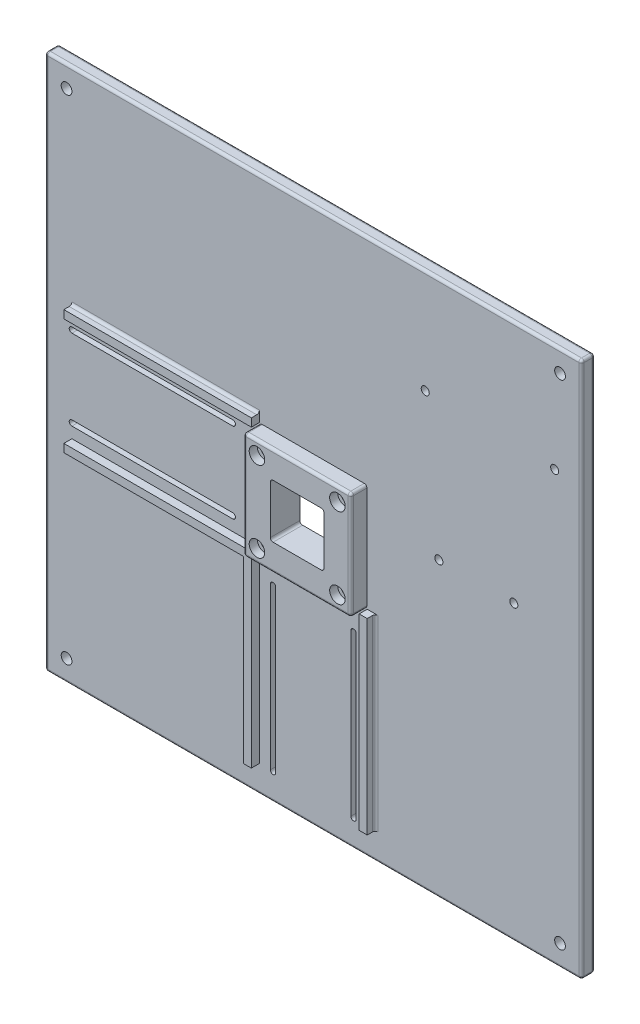
SolidWorks part; units mm, degrees
ref_plane "Plan de face" through (0, 0, 0) normal (0, 0, 1) x (1, 0, 0)
ref_plane "Plan de dessus" through (0, 0, 0) normal (0, 1, 0) x (1, 0, 0)
ref_plane "Plan de droite" through (0, 0, 0) normal (1, 0, 0) x (0, 0, -1)
sketch "Esquisse1" plane through (0, 0, 0) normal (0, 0, 1) x (1, 0, 0)
  line L1 (-100, 100) -> (100, 100)
  line L2 (-100, 100) -> (-100, -100)
  line L3 (-100, -100) -> (100, -100)
  line L4 (100, 100) -> (100, -100)
  dimension "D1" = 100
  dimension "D2" = 200
  dimension "D3" = 100
  dimension "D4" = 200
extrude "Boss.-Extru.1" add sketch "Esquisse1" along normal blind 5
fillet "Congé1" radius 1 12 edges at (0, -100, 5) (-100, 0, 5) (0, 100, 5) (100, 0, 5) (-100, -100, 2.5) (100, -100, 2.5) (-100, 100, 2.5) (100, 100, 2.5) (0, -100, 0) (-100, 0, 0) (0, 100, 0) (100, 0, 0)
sketch "Esquisse4" plane through (0, 0, 5) normal (0, 0, 1) x (1, 0, 0)
  line L1 (-10, 10) -> (10, 10)
  line L2 (-10, 10) -> (-10, -10)
  line L3 (-10, -10) -> (10, -10)
  line L4 (10, 10) -> (10, -10)
  circle A0 centre (-15, 15) radius 1.5
  circle A1 centre (15, 15) radius 1.5
  circle A2 centre (15, -15) radius 1.5
  circle A3 centre (-15, -15) radius 1.5
  point P4 (0, 0)
  dimension "D5" = 3
  dimension "D1" = 10
  dimension "D2" = 20
  dimension "D3" = 10
  dimension "D4" = 20
  dimension "D6" = 5
  dimension "D7" = 5
  dimension "D8" = 5
  dimension "D9" = 5
sketch "Esquisse9" plane through (0, 0, 0) normal (0, 0, -1) x (-1, 0, 0)
  line L0 (-100, -100) -> (-100, 100) construction
  line L1 (100, -100) -> (-100, -100) construction
  line L2 (-100, 100) -> (100, 100) construction
  line L3 (100, 100) -> (100, -100) construction
  circle A0 centre (-92, 92) radius 2
  circle A1 centre (92, 92) radius 2
  circle A2 centre (92, -92) radius 2
  circle A3 centre (-92, -92) radius 2
  dimension "D2" = 4
  dimension "D5" = 8
  dimension "D6" = 8
  dimension "D7" = 8
  dimension "D8" = 8
extrude "Enlèv. mat.-Extru.4" cut sketch "Esquisse9" against normal up to next
extrude "Enlèv. mat.-Extru.5" cut sketch "Esquisse4" against normal through all and the other way through all
sketch "Esquisse11" plane through (0, 0, 5) normal (0, 0, 1) x (1, 0, 0)
  line L0 (-10, -10) -> (10, -10) construction
  line L1 (-20, -20) -> (20, -20)
  line L2 (-20, -20) -> (-20, 20)
  line L3 (-20, 20) -> (20, 20)
  line L4 (20, -20) -> (20, 20)
  line L5 (-10, 10) -> (-10, -10) construction
  line L6 (10, 10) -> (-10, 10) construction
  line L7 (10, -10) -> (10, 10) construction
  dimension "D1" = 10
  dimension "D2" = 10
  dimension "D3" = 10
  dimension "D4" = 10
extrude "Boss.-Extru.3" add sketch "Esquisse11" along normal blind 6 contours L2 L3 L4 L1
fillet "Congé2" radius 1 12 edges at (10, -10, 2.5) (-10, -10, 2.5) (10, 10, 2.5) (-10, 10, 2.5) (-20, 0, 11) (0, 20, 11) (20, 0, 11) (0, -20, 11) (20, 20, 8) (20, -20, 8) (-20, -20, 8) (-20, 20, 8)
sketch "Esquisse12" plane through (0, 0, 11) normal (0, 0, 1) x (1, 0, 0)
  line L0 (-9, -10) -> (9, -10) construction
  line L1 (-9, -10) -> (9, -10)
  line L4 (19, 19) -> (-19, 19)
  line L5 (19, 19) -> (-19, 19)
  line L6 (-19, 19) -> (-19, -19)
  line L7 (-19, 19) -> (-19, -19)
  line L12 (10, -9) -> (10, 9)
  line L13 (-9, -10) -> (9, -10)
  line L14 (-10, 9) -> (-10, -9)
  line L15 (9, 10) -> (-9, 10)
  line L16 (10, -9) -> (10, 9)
  line L17 (-9, -10) -> (9, -10)
  line L18 (-10, 9) -> (-10, -9)
  line L19 (9, 10) -> (-9, 10)
  line L22 (-19, -19) -> (19, -19)
  line L23 (-19, -19) -> (19, -19)
  line L24 (19, -19) -> (19, 19)
  line L25 (19, -19) -> (19, 19)
  circle A0 centre (-15, -15) radius 1.5 construction
  circle A1 centre (15, -15) radius 1.5 construction
  circle A2 centre (15, 15) radius 1.5 construction
  circle A3 centre (-15, 15) radius 1.5 construction
  circle A4 centre (-15, -15) radius 1.5
  circle A5 centre (15, -15) radius 1.5
  circle A6 centre (15, 15) radius 1.5
  circle A7 centre (-15, 15) radius 1.5
  arc A12 (9, -10) -> (10, -9) centre (9, -9) ccw
  arc A13 (-10, -9) -> (-9, -10) centre (-9, -9) ccw
  arc A14 (-9, 10) -> (-10, 9) centre (-9, 9) ccw
  arc A15 (10, 9) -> (9, 10) centre (9, 9) ccw
  arc A16 (9, -10) -> (10, -9) centre (9, -9) ccw
  arc A17 (-10, -9) -> (-9, -10) centre (-9, -9) ccw
  arc A18 (-9, 10) -> (-10, 9) centre (-9, 9) ccw
  arc A19 (10, 9) -> (9, 10) centre (9, 9) ccw
  dimension "D1" = 0
  dimension "D2" = 0
extrude "Enlèv. mat.-Extru.6" cut sketch "Esquisse12" against normal through all contours L16 A19 L19 A18 L18 A17 L1 A16 | A6 | A7 | A5 | A4
sketch "Esquisse13" plane through (0, 0, 11) normal (0, 0, 1) x (1, 0, 0)
  circle A0 centre (-15, 15) radius 2.9
  circle A1 centre (15, 15) radius 2.9
  circle A2 centre (15, -15) radius 2.9
  circle A3 centre (-15, -15) radius 2.9
  dimension "D1" = 5.8
extrude "Enlèv. mat.-Extru.7" cut sketch "Esquisse13" against normal blind 3
sketch "Esquisse14" plane through (0, 0, 5) normal (0, 0, 1) x (1, 0, 0)
  line L0 (-90, 15) -> (-30, 15) construction
  line L1 (-90, 16) -> (-30, 16)
  line L2 (-90, 14) -> (-30, 14)
  line L3 (-100, -99) -> (-100, 99) construction
  line L4 (-20, -19) -> (-20, 19) construction
  line L5 (-30, -15) -> (-90, -15) construction
  line L6 (-30, -16) -> (-90, -16)
  line L7 (-30, -14) -> (-90, -14)
  line L8 (15, -30) -> (15, -90) construction
  line L9 (16, -30) -> (16, -90)
  line L10 (14, -30) -> (14, -90)
  line L11 (-15, -90) -> (-15, -30) construction
  line L12 (-16, -90) -> (-16, -30)
  line L13 (-14, -90) -> (-14, -30)
  line L14 (-19, -20) -> (19, -20) construction
  line L15 (99, -100) -> (-99, -100) construction
  arc A0 (-90, 16) -> (-90, 14) centre (-90, 15) ccw
  arc A1 (-30, 14) -> (-30, 16) centre (-30, 15) ccw
  arc A2 (-30, -16) -> (-30, -14) centre (-30, -15) ccw
  arc A3 (-90, -14) -> (-90, -16) centre (-90, -15) ccw
  arc A4 (16, -30) -> (14, -30) centre (15, -30) ccw
  arc A5 (14, -90) -> (16, -90) centre (15, -90) ccw
  arc A6 (-16, -90) -> (-14, -90) centre (-15, -90) ccw
  arc A7 (-14, -30) -> (-16, -30) centre (-15, -30) ccw
  point P2 (-60, 15)
  point P11 (-20, 0)
  point P14 (-60, -15)
  point P21 (15, -60)
  point P26 (-15, -60)
  point P33 (0, -20)
  dimension "D1" = 2
  dimension "D2" = 10
  dimension "D3" = 10
  dimension "D4" = 15
  dimension "D5" = 2
  dimension "D6" = 10
  dimension "D7" = 10
  dimension "D8" = 30
  dimension "D9" = 2
  dimension "D10" = 2
  dimension "D11" = 15
  dimension "D12" = 30
  dimension "D13" = 10
  dimension "D14" = 10
  dimension "D15" = 10
  dimension "D16" = 10
extrude "Enlèv. mat.-Extru.8" cut sketch "Esquisse14" against normal through all
sketch "Esquisse15" plane through (0, 0, 5) normal (0, 0, 1) x (1, 0, 0)
  line L0 (-20.1, -20.1) -> (-20.1, -90)
  line L1 (-20.1, 20.1) -> (-90, 20.1)
  line L2 (-20.1, 20.1) -> (-20.1, 23.1)
  line L3 (-20.1, 23.1) -> (-90, 23.1)
  line L4 (-90, 20.1) -> (-90, 23.1)
  line L5 (-20.1, -20.1) -> (-90, -20.1)
  line L7 (-23.1, -23.1) -> (-90, -23.1)
  line L8 (-90, -20.1) -> (-90, -23.1)
  line L9 (-20.1, -90) -> (-23.1, -90)
  line L10 (-23.1, -90) -> (-23.1, -23.1)
  line L12 (23.1, -20.1) -> (20.1, -20.1)
  line L13 (23.1, -20.1) -> (23.1, -90)
  line L14 (23.1, -90) -> (20.1, -90)
  line L15 (20.1, -20.1) -> (20.1, -90)
  dimension "D1" = 3
  dimension "D2" = 3
  dimension "D3" = 3
  dimension "D4" = 3
  dimension "D5" = 20.1
  dimension "D6" = 40.2
  dimension "D7" = 20.1
  dimension "D8" = 40.2
extrude "Boss.-Extru.4" add sketch "Esquisse15" along normal blind 3
fillet "Congé3" radius 1 4 edges at (-55.05, 23.1, 5) (-56.55, -23.1, 5) (-23.1, -56.55, 5) (23.1, -55.05, 5)
sketch "Esquisse20" plane through (0, 0, 5) normal (0, 0, 1) x (1, 0, 0)
  line L0 (-99, 100) -> (99, 100) construction
  line L1 (100, 99) -> (100, -99) construction
  circle A1 centre (46.82, 9.2) radius 1.5
  circle A5 centre (41.74, 61.27) radius 1.5
  circle A6 centre (90, 60) radius 1.5
  circle A7 centre (74.76, 9.2) radius 1.5
  dimension "D1" = 3
  dimension "D2" = 3
  dimension "D3" = 3
  dimension "D4" = 3
  dimension "D6" = 48.26
  dimension "D8" = 15.24
  dimension "D9" = 1.27
  dimension "D10" = 40
  dimension "D11" = 10
  dimension "D5" = 27.94
  dimension "D7" = 50.8
extrude "Enlèv. mat.-Extru.12" cut sketch "Esquisse20" against normal blind 10
